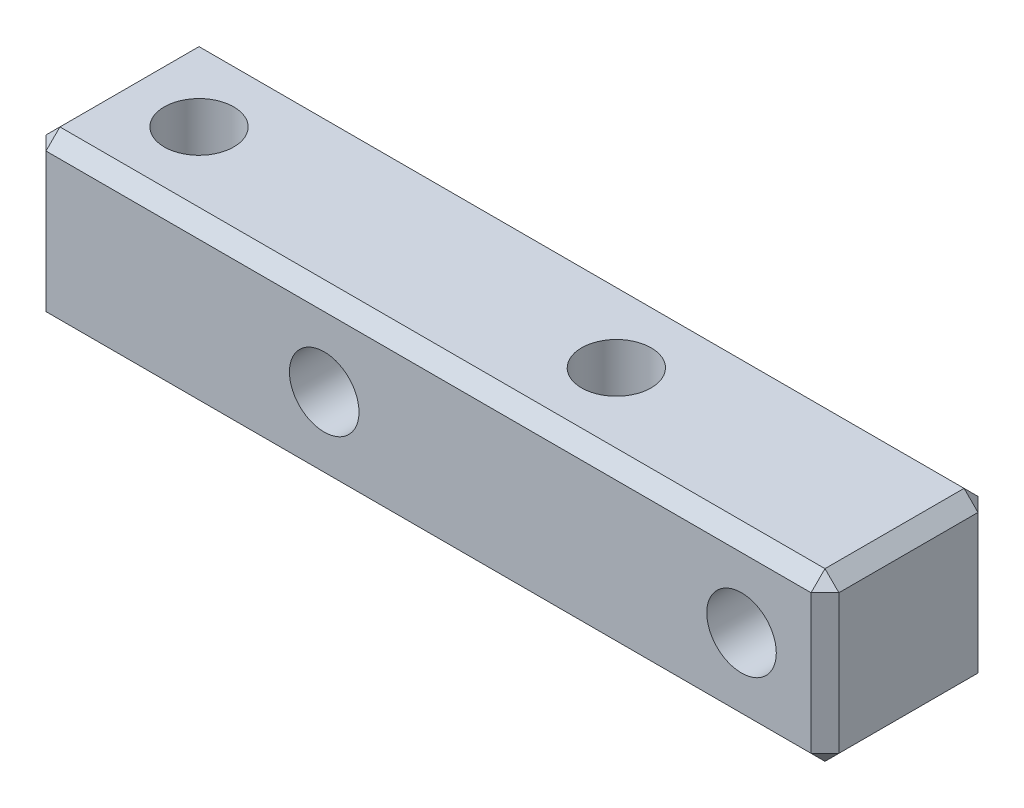
SolidWorks part; units mm, degrees
material "6061 合金"
ref_plane "前视基准面" through (0, 0, 0) normal (0, 0, 1) x (1, 0, 0)
ref_plane "上视基准面" through (0, 0, 0) normal (0, 1, 0) x (1, 0, 0)
ref_plane "右视基准面" through (0, 0, 0) normal (1, 0, 0) x (0, 0, -1)
sketch "草图2" plane through (0, 0, 0) normal (0, 0, 1) x (1, 0, 0)
  line L10 (3, 3) -> (3, -3)
  line L11 (0, 0) -> (-15, 0) construction
  line L41 (3, -3) -> (-25.5, -3)
  line L48 (-25.5, 3) -> (3, 3)
  line L49 (-25.5, 3) -> (-25.5, -3)
  circle A3 centre (-15, 0) radius 0.5
  circle A5 centre (0, 0) radius 0.5
  dimension "D1" = 15
  dimension "D2" = 1
  dimension "D3" = 3
  dimension "D4" = 10.5
  dimension "D7" = 3
  dimension "D6" = 3
extrude "凸台-拉伸1" add sketch "草图2" along normal mid plane 6
hole_wizard "M3 螺纹孔1" positions "草图5" profile "草图4" tap size "M3" standard "GB" end condition through all
sketch "草图5" plane through (0, 0, 3) normal (0, 0, 1) x (1, 0, 0)
  point P0 (0, 0)
  point P3 (-15, 0)
sketch "草图4" plane through (0, 0, 3) normal (1, 0, 0) x (0, -1, 0)
  line L0 (0, 0) -> (0, 6)
  line L1 (0, 6) -> (1.25, 6)
  line L2 (1.25, 6) -> (1.25, 0)
  line L5 (1.25, 0) -> (0, 0)
  line L11 (0, -6.35) -> (0, 107.95) construction
  dimension "通孔螺纹孔钻头直径" = 2.5
  dimension "通孔螺纹孔钻头深度" = 6
cosmetic thread "孔螺蚊线3" parameters "D2"=3
cosmetic thread "孔螺蚊线4" parameters "D2"=3
hole_wizard "M3 螺纹孔2" positions "草图6" profile "草图7" tap size "M3" standard "GB" end condition through all
sketch "草图6" plane through (0, 3, 0) normal (0, 1, 0) x (1, 0, 0)
  line L1 (-22.5, 0) -> (0, 0) construction
  line L2 (-25.5, -3) -> (-25.5, 3) construction
  point P0 (-7.5, 0)
  point P2 (-22.5, 0)
  dimension "D1" = 3
  dimension "D2" = 15
sketch "草图7" plane through (-7.5, 3, 0) normal (1, 0, 0) x (0, 0, 1)
  line L0 (0, 0) -> (0, 6)
  line L1 (0, 6) -> (1.25, 6)
  line L2 (1.25, 6) -> (1.25, 0)
  line L5 (1.25, 0) -> (0, 0)
  line L11 (0, -6.35) -> (0, 107.95) construction
  dimension "通孔螺纹孔钻头直径" = 2.5
  dimension "通孔螺纹孔钻头深度" = 6
cosmetic thread "孔螺蚊线5" parameters "D2"=3
cosmetic thread "孔螺蚊线6" parameters "D2"=3
chamfer "倒角1" distance 0.5 angle 45 12 edges at (-11.25, -3, -3) (-11.25, -3, 3) (-25.5, 0, -3) (-25.5, 0, 3) (3, -3, 0) (3, 0, 3) (3, 0, -3) (-11.25, 3, -3) (3, 3, 0) (-11.25, 3, 3) (-25.5, 3, 0) (-25.5, -3, 0)
